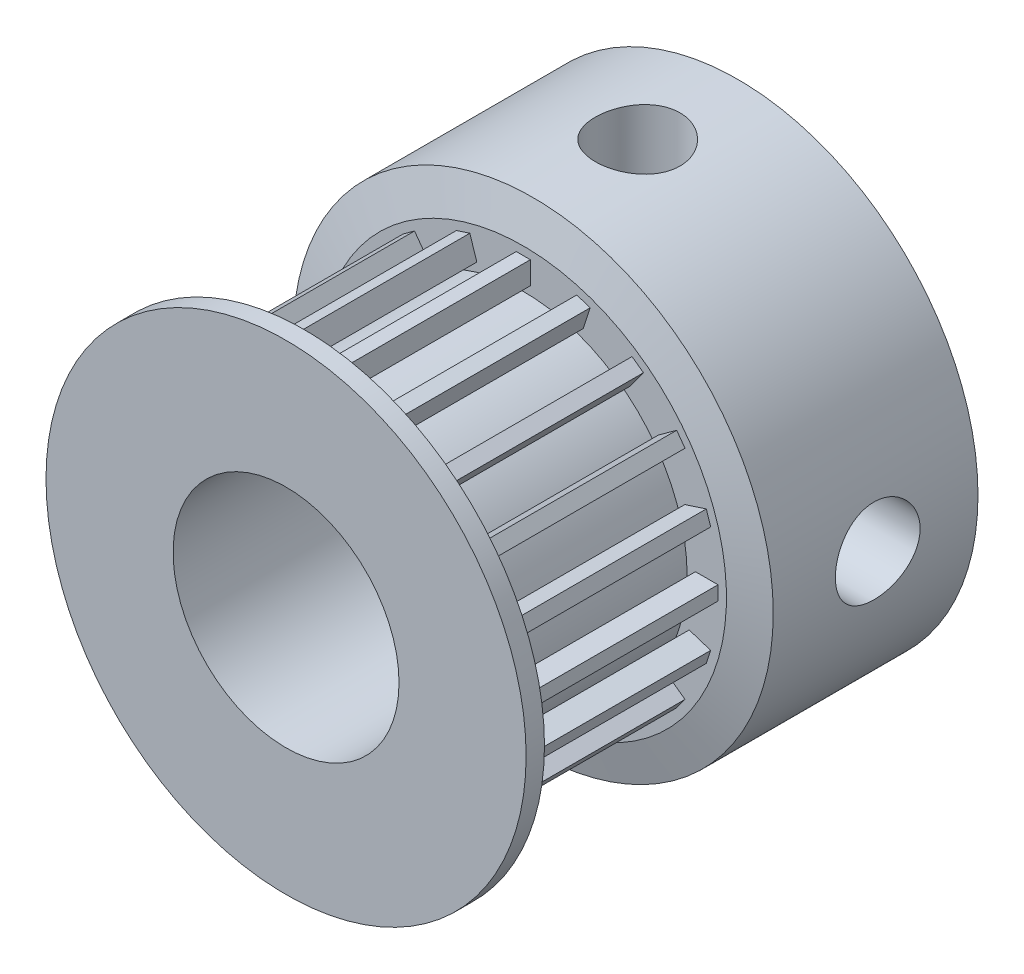
SolidWorks part; units mm, degrees
ref_plane "Front Plane" through (0, 0, 0) normal (0, 0, 1) x (1, 0, 0)
ref_plane "Top Plane" through (0, 0, 0) normal (0, 1, 0) x (1, 0, 0)
ref_plane "Right Plane" through (0, 0, 0) normal (1, 0, 0) x (0, 0, -1)
sketch "Sketch2" plane through (0, 0, 0) normal (1, 0, 0) x (0, 0, -1)
  line L0 (-16, 4) -> (0, 4)
  line L1 (0, 4) -> (0, 8.5)
  line L2 (0, 8.5) -> (-7.6, 8.5)
  line L3 (-7.6, 8.5) -> (-7.6, 5.8)
  line L4 (-7.6, 5.8) -> (-15, 5.8)
  line L5 (-15, 5.8) -> (-15, 8.5)
  line L6 (-15, 8.5) -> (-16, 8.5)
  line L7 (-16, 8.5) -> (-16, 4)
  line L8 (-79.6095, 0) -> (75.5553, 0) construction
  dimension "D1" = 16
  dimension "D2" = 8.5
  dimension "D3" = 1
  dimension "D4" = 7.4
  dimension "D5" = 4
  dimension "D6" = 5.8
revolve "Revolve1" add sketch "Sketch2" angle 360 about L8
chamfer "Chamfer1" distance 0.35 angle 75 1 edges at (8.5, 0, 15)
chamfer "Chamfer2" distance 0.35 angle 75 1 edges at (8.5, 0, 7.6)
sketch "Sketch4" plane through (0, 0, 7.6) normal (0, 0, 1) x (1, 0, 0)
  line L0 (1.6457, 5.8738) -> (1.8929, 6.6347)
  line L1 (1.8929, 6.6347) -> (2.3684, 6.4802)
  line L2 (-0.25, 6.0949) -> (-0.25, 6.8949)
  line L3 (-0.25, 6.8949) -> (0.25, 6.8949)
  line L4 (0.25, 6.0949) -> (0.25, 6.8949)
  line L5 (2.1212, 5.7193) -> (2.3684, 6.4802)
  line L6 (3.3802, 5.0778) -> (3.8505, 5.725)
  line L7 (3.8505, 5.725) -> (4.255, 5.4311)
  line L8 (3.7847, 4.7839) -> (4.255, 5.4311)
  line L9 (4.7839, 3.7847) -> (5.4311, 4.255)
  line L10 (5.4311, 4.255) -> (5.725, 3.8505)
  line L11 (5.0778, 3.3802) -> (5.725, 3.8505)
  line L12 (5.7193, 2.1212) -> (6.4802, 2.3684)
  line L13 (6.4802, 2.3684) -> (6.6347, 1.8929)
  line L14 (5.8738, 1.6457) -> (6.6347, 1.8929)
  line L15 (6.0949, 0.25) -> (6.8949, 0.25)
  line L16 (6.8949, 0.25) -> (6.8949, -0.25)
  line L17 (6.0949, -0.25) -> (6.8949, -0.25)
  line L18 (5.8738, -1.6457) -> (6.6347, -1.8929)
  line L19 (6.6347, -1.8929) -> (6.4802, -2.3684)
  line L20 (5.7193, -2.1212) -> (6.4802, -2.3684)
  line L21 (5.0778, -3.3802) -> (5.725, -3.8505)
  line L22 (5.725, -3.8505) -> (5.4311, -4.255)
  line L23 (4.7839, -3.7847) -> (5.4311, -4.255)
  line L24 (3.7847, -4.7839) -> (4.255, -5.4311)
  line L25 (4.255, -5.4311) -> (3.8505, -5.725)
  line L26 (3.3802, -5.0778) -> (3.8505, -5.725)
  line L27 (2.1212, -5.7193) -> (2.3684, -6.4802)
  line L28 (2.3684, -6.4802) -> (1.8929, -6.6347)
  line L29 (1.6457, -5.8738) -> (1.8929, -6.6347)
  line L30 (0.25, -6.0949) -> (0.25, -6.8949)
  line L31 (0.25, -6.8949) -> (-0.25, -6.8949)
  line L32 (-0.25, -6.0949) -> (-0.25, -6.8949)
  line L33 (-1.6457, -5.8738) -> (-1.8929, -6.6347)
  line L34 (-1.8929, -6.6347) -> (-2.3684, -6.4802)
  line L35 (-2.1212, -5.7193) -> (-2.3684, -6.4802)
  line L36 (-3.3802, -5.0778) -> (-3.8505, -5.725)
  line L37 (-3.8505, -5.725) -> (-4.255, -5.4311)
  line L38 (-3.7847, -4.7839) -> (-4.255, -5.4311)
  line L39 (-4.7839, -3.7847) -> (-5.4311, -4.255)
  line L40 (-5.4311, -4.255) -> (-5.725, -3.8505)
  line L41 (-5.0778, -3.3802) -> (-5.725, -3.8505)
  line L42 (-5.7193, -2.1212) -> (-6.4802, -2.3684)
  line L43 (-6.4802, -2.3684) -> (-6.6347, -1.8929)
  line L44 (-5.8738, -1.6457) -> (-6.6347, -1.8929)
  line L45 (-6.0949, -0.25) -> (-6.8949, -0.25)
  line L46 (-6.8949, -0.25) -> (-6.8949, 0.25)
  line L47 (-6.0949, 0.25) -> (-6.8949, 0.25)
  line L48 (-5.8738, 1.6457) -> (-6.6347, 1.8929)
  line L49 (-6.6347, 1.8929) -> (-6.4802, 2.3684)
  line L50 (-5.7193, 2.1212) -> (-6.4802, 2.3684)
  line L51 (-5.0778, 3.3802) -> (-5.725, 3.8505)
  line L52 (-5.725, 3.8505) -> (-5.4311, 4.255)
  line L53 (-4.7839, 3.7847) -> (-5.4311, 4.255)
  line L54 (-3.7847, 4.7839) -> (-4.255, 5.4311)
  line L55 (-4.255, 5.4311) -> (-3.8505, 5.725)
  line L56 (-3.3802, 5.0778) -> (-3.8505, 5.725)
  line L57 (-2.1212, 5.7193) -> (-2.3684, 6.4802)
  line L58 (-2.3684, 6.4802) -> (-1.8929, 6.6347)
  line L59 (-1.6457, 5.8738) -> (-1.8929, 6.6347)
  arc A0 (-3.3802, 5.0778) -> (-3.7847, 4.7839) centre (0, 0) ccw
  arc A1 (-1.6457, 5.8738) -> (-2.1212, 5.7193) centre (0, 0) ccw
  arc A2 (0.25, 6.0949) -> (-0.25, 6.0949) centre (0, 0) ccw
  arc A3 (2.1212, 5.7193) -> (1.6457, 5.8738) centre (0, 0) ccw
  arc A4 (3.7847, 4.7839) -> (3.3802, 5.0778) centre (0, 0) ccw
  arc A5 (5.0778, 3.3802) -> (4.7839, 3.7847) centre (0, 0) ccw
  arc A6 (5.8738, 1.6457) -> (5.7193, 2.1212) centre (0, 0) ccw
  arc A7 (6.0949, -0.25) -> (6.0949, 0.25) centre (0, 0) ccw
  arc A8 (5.7193, -2.1212) -> (5.8738, -1.6457) centre (0, 0) ccw
  arc A9 (4.7839, -3.7847) -> (5.0778, -3.3802) centre (0, 0) ccw
  arc A10 (3.3802, -5.0778) -> (3.7847, -4.7839) centre (0, 0) ccw
  arc A11 (1.6457, -5.8738) -> (2.1212, -5.7193) centre (0, 0) ccw
  arc A12 (-0.25, -6.0949) -> (0.25, -6.0949) centre (0, 0) ccw
  arc A13 (-2.1212, -5.7193) -> (-1.6457, -5.8738) centre (0, 0) ccw
  arc A14 (-3.7847, -4.7839) -> (-3.3802, -5.0778) centre (0, 0) ccw
  arc A15 (-5.0778, -3.3802) -> (-4.7839, -3.7847) centre (0, 0) ccw
  arc A16 (-5.8738, -1.6457) -> (-5.7193, -2.1212) centre (0, 0) ccw
  arc A17 (-6.0949, 0.25) -> (-6.0949, -0.25) centre (0, 0) ccw
  arc A18 (-5.7193, 2.1212) -> (-5.8738, 1.6457) centre (0, 0) ccw
  arc A19 (-4.7839, 3.7847) -> (-5.0778, 3.3802) centre (0, 0) ccw
  dimension "D1" = 12.2
  dimension "D2" = 0.5
  dimension "D3" = 0.25
  dimension "D4" = 0.8
  dimension "D5" = 20
extrude "Boss-Extrude1" add sketch "Sketch4" along normal up to surface (7.4 mm away) up to face at (7.1938, 0, 15)
ref_plane "Plane1" through (0, 8.9, 0) normal (0, 1, 0) x (-1, 0, 0)
sketch "Sketch6" plane through (0, 8.9, 0) normal (0, 1, 0) x (-1, 0, 0)
  line L2 (0, 3.55) -> (4.2063, 3.55) construction
  circle A0 centre (0, 3.55) radius 1.5
  dimension "D1" = 3
  dimension "D2" = 3.55
extrude "Cut-Extrude1" cut sketch "Sketch6" against normal blind 10
pattern_circular "CirPattern1" count 2 every 270 about axis through (0, 0, 0) along (0, 0, 1) of "Cut-Extrude1"
